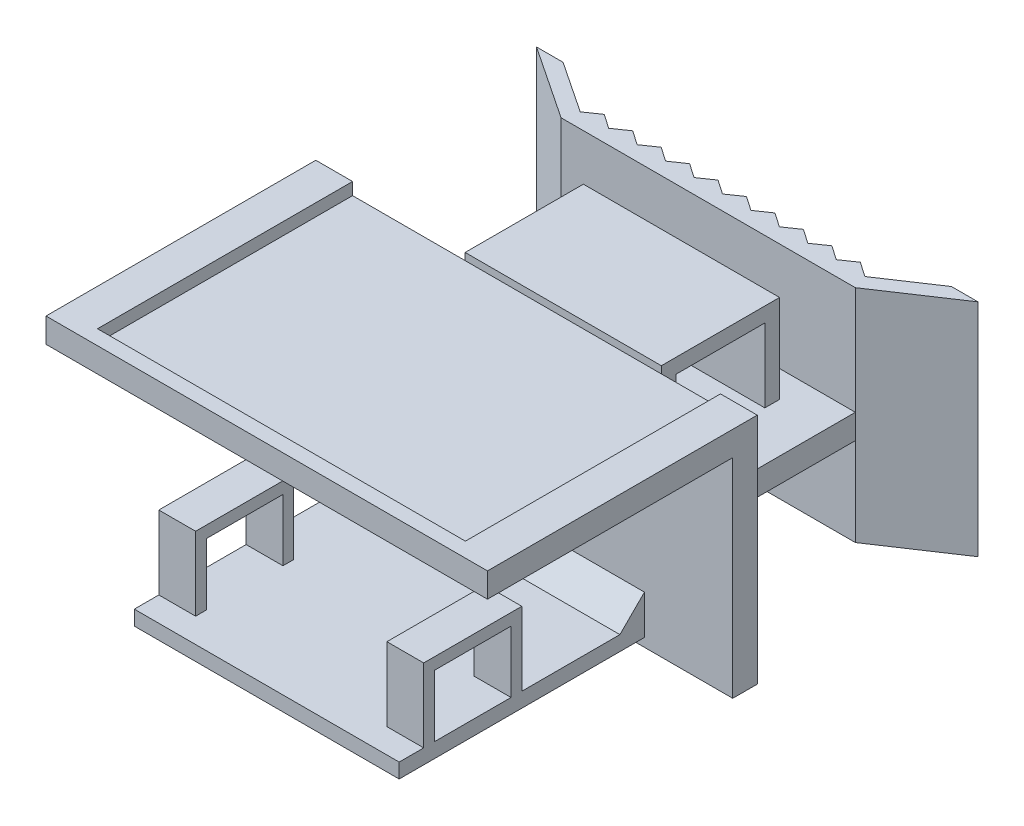
SolidWorks part; units mm, degrees
ref_plane "Alzado" through (0, 0, 0) normal (0, 0, 1) x (1, 0, 0)
ref_plane "Planta" through (0, 0, 0) normal (0, 1, 0) x (1, 0, 0)
ref_plane "Vista lateral" through (0, 0, 0) normal (1, 0, 0) x (0, 0, -1)
sketch "Croquis1" plane through (0, 0, 0) normal (0, 1, 0) x (1, 0, 0)
  line L1 (-45, 25) -> (45, 25)
  line L2 (-45, 25) -> (-45, -25)
  line L3 (-45, -25) -> (45, -25)
  line L4 (45, 25) -> (45, -25)
  line L5 (-45, 25) -> (45, -25) construction
  line L6 (-45, -25) -> (45, 25) construction
  point P0 (0, 0)
  dimension "D1" = 50
  dimension "D2" = 90
extrude "Saliente-Extruir1" add sketch "Croquis1" along normal blind 5
sketch "Croquis4" plane through (0, 5, 0) normal (0, 1, 0) x (1, 0, 0)
  line L0 (45, -25) -> (45, 25) construction
  line L1 (-45, 25) -> (45, 25)
  line L2 (-45, 25) -> (-45, 30)
  line L3 (-45, 30) -> (45, 30)
  line L4 (45, 25) -> (45, 30)
  dimension "D1" = 5
extrude "Saliente-Extruir2" add sketch "Croquis4" against normal blind 49.5
sketch "Croquis5" plane through (0, 0, -30) normal (0, 0, -1) x (-1, 0, 0)
  line L0 (-45, -44.5) -> (45, -44.5) construction
  line L1 (-30, -19.5) -> (30, -19.5)
  line L2 (-30, -19.5) -> (-30, -24.5)
  line L3 (-30, -24.5) -> (30, -24.5)
  line L4 (30, -19.5) -> (30, -24.5)
  line L5 (-30, -19.5) -> (30, -24.5) construction
  line L6 (-30, -24.5) -> (30, -19.5) construction
  point P0 (0, -22)
  dimension "D1" = 60
  dimension "D2" = 5
  dimension "D3" = 20
extrude "Saliente-Extruir3" add sketch "Croquis5" along normal blind 35
sketch "Croquis7" plane through (0, -19.5, 0) normal (0, 1, 0) x (1, 0, 0)
  line L4 (-30, 30) -> (30, 30)
  line L5 (30, 30) -> (30, 65)
  line L6 (30, 65) -> (-30, 65)
  line L7 (-30, 65) -> (-30, 30)
  line L8 (-30, 30) -> (30, 30)
  line L9 (30, 30) -> (30, 65)
  line L10 (30, 65) -> (-30, 65)
  line L11 (-30, 65) -> (-30, 30)
  dimension "D1" = 0
sketch "Croquis11" plane through (0, 5, 0) normal (0, 1, 0) x (1, 0, 0)
  line L1 (-37.5, 58) -> (37.5, 58)
  line L2 (-37.5, 58) -> (-37.5, -22)
  line L3 (-37.5, -22) -> (37.5, -22)
  line L4 (37.5, 58) -> (37.5, -22)
  line L6 (-45, -25) -> (45, -25) construction
  point P4 (0, -22)
  dimension "D1" = 75
  dimension "D2" = 80
  dimension "D3" = 3
extrude "Cortar-Extruir3" cut sketch "Croquis11" against normal blind 2.5
sketch "Croquis12" plane through (0, -19.5, 0) normal (0, 1, 0) x (1, 0, 0)
  line L0 (-45, 30) -> (-45, -25) construction
  line L1 (-45, 65) -> (45, 65) construction
  line L2 (-45, 65) -> (-45, 75) construction
  line L3 (-45, 75) -> (-39.5917, 75) construction
  line L4 (45, 65) -> (45, 75) construction
  line L5 (45, -25) -> (45, 30) construction
  line L6 (30, 65) -> (-30, 65) construction
  line L7 (-45, 75) -> (-30, 65)
  line L8 (30, 65) -> (45, 75)
  line L9 (-30, 65) -> (30, 65)
  line L10 (-39.5917, 75) -> (-29.0917, 68)
  line L11 (-29.0917, 68) -> (29.0917, 68)
  line L12 (29.0917, 68) -> (39.5917, 75)
  line L13 (-45, 75) -> (-39.5917, 75)
  line L14 (-43.3359, 77.4962) -> (-29.0917, 68) construction
  line L15 (39.5917, 75) -> (45, 75) construction
  line L16 (39.5917, 75) -> (45, 75)
  line L17 (29.0917, 68) -> (43.3359, 77.4962) construction
  line L18 (-29.0917, 68) -> (-26.1917, 70)
  line L19 (-26.1917, 70) -> (-23.2917, 68)
  line L20 (0, 68) -> (0, 75) construction
  line L21 (-20.3917, 70) -> (-17.4917, 68)
  line L22 (-23.2917, 68) -> (-20.3917, 70)
  line L23 (-14.5917, 70) -> (-11.6917, 68)
  line L24 (-17.4917, 68) -> (-14.5917, 70)
  line L25 (-8.7917, 70) -> (-5.8917, 68)
  line L26 (-11.6917, 68) -> (-8.7917, 70)
  line L27 (-2.9917, 70) -> (-0.0917, 68)
  line L28 (-5.8917, 68) -> (-2.9917, 70)
  line L29 (2.8083, 70) -> (5.7083, 68)
  line L30 (-0.0917, 68) -> (2.8083, 70)
  line L31 (8.6083, 70) -> (11.5083, 68)
  line L32 (5.7083, 68) -> (8.6083, 70)
  line L33 (14.4083, 70) -> (17.3083, 68)
  line L34 (11.5083, 68) -> (14.4083, 70)
  line L35 (20.2083, 70) -> (23.1083, 68)
  line L36 (17.3083, 68) -> (20.2083, 70)
  line L37 (26.0083, 70) -> (28.9083, 68)
  line L38 (23.1083, 68) -> (26.0083, 70)
  line M15 (30, 65) -> (-30, 65)
  dimension "D1" = 10
  dimension "D2" = 3
  dimension "D3" = 2
  dimension "D4" = 2.9
  dimension "D5" = 2.9
  dimension "D6" = 10
extrude "Saliente-Extruir4" add sketch "Croquis12" against normal up to surface and the other way up to surface contours L16 L12 L11 L10 L13 L7 L8 M15 | L19 L18 L11 | L22 L11 L21 | L24 L11 L23 | L28 L11 L27 | L30 L11 L29 | L26 L11 L25 | L32 L11 L31 | L34 L11 L33 | L36 L11 L35 | L38 L11 L37
sketch "Croquis13" plane through (0, -44.5, 0) normal (0, -1, 0) x (1, 0, 0)
  line L4 (-45, -25) -> (-45, -30)
  line L5 (-45, -30) -> (45, -30)
  line L6 (45, -30) -> (45, -25)
  line L7 (45, -25) -> (-45, -25)
  line L8 (-45, -25) -> (-45, -30)
  line L9 (-45, -30) -> (45, -30)
  line L10 (45, -30) -> (45, -25)
  line L11 (45, -25) -> (-45, -25)
  line L36 (-39.5917, -75) -> (-29.0917, -68)
  line L37 (-29.0917, -68) -> (-26.1917, -70)
  line L38 (-26.1917, -70) -> (-23.2917, -68)
  line L39 (-23.2917, -68) -> (-20.3917, -70)
  line L40 (-20.3917, -70) -> (-17.4917, -68)
  line L41 (-17.4917, -68) -> (-14.5917, -70)
  line L42 (-14.5917, -70) -> (-11.6917, -68)
  line L43 (-11.6917, -68) -> (-8.7917, -70)
  line L44 (-8.7917, -70) -> (-5.8917, -68)
  line L45 (-5.8917, -68) -> (-2.9917, -70)
  line L46 (-2.9917, -70) -> (-0.0917, -68)
  line L47 (-0.0917, -68) -> (2.8083, -70)
  line L48 (2.8083, -70) -> (5.7083, -68)
  line L49 (5.7083, -68) -> (8.6083, -70)
  line L50 (8.6083, -70) -> (11.5083, -68)
  line L51 (11.5083, -68) -> (14.4083, -70)
  line L52 (14.4083, -70) -> (17.3083, -68)
  line L53 (17.3083, -68) -> (20.2083, -70)
  line L54 (20.2083, -70) -> (23.1083, -68)
  line L55 (23.1083, -68) -> (26.0083, -70)
  line L56 (26.0083, -70) -> (28.9083, -68)
  line L57 (28.9083, -68) -> (29.0917, -68)
  line L58 (29.0917, -68) -> (39.5917, -75)
  line L59 (39.5917, -75) -> (45, -75)
  line L60 (45, -75) -> (30, -65)
  line L61 (30, -65) -> (-30, -65)
  line L62 (-30, -65) -> (-45, -75)
  line L63 (-45, -75) -> (-39.5917, -75)
  line L64 (-39.5917, -75) -> (-29.0917, -68)
  line L65 (-29.0917, -68) -> (-26.1917, -70)
  line L66 (-26.1917, -70) -> (-23.2917, -68)
  line L67 (-23.2917, -68) -> (-20.3917, -70)
  line L68 (-20.3917, -70) -> (-17.4917, -68)
  line L69 (-17.4917, -68) -> (-14.5917, -70)
  line L70 (-14.5917, -70) -> (-11.6917, -68)
  line L71 (-11.6917, -68) -> (-8.7917, -70)
  line L72 (-8.7917, -70) -> (-5.8917, -68)
  line L73 (-5.8917, -68) -> (-2.9917, -70)
  line L74 (-2.9917, -70) -> (-0.0917, -68)
  line L75 (-0.0917, -68) -> (2.8083, -70)
  line L76 (2.8083, -70) -> (5.7083, -68)
  line L77 (5.7083, -68) -> (8.6083, -70)
  line L78 (8.6083, -70) -> (11.5083, -68)
  line L79 (11.5083, -68) -> (14.4083, -70)
  line L80 (14.4083, -70) -> (17.3083, -68)
  line L81 (17.3083, -68) -> (20.2083, -70)
  line L82 (20.2083, -70) -> (23.1083, -68)
  line L83 (23.1083, -68) -> (26.0083, -70)
  line L84 (26.0083, -70) -> (28.9083, -68)
  line L85 (28.9083, -68) -> (29.0917, -68)
  line L86 (29.0917, -68) -> (39.5917, -75)
  line L87 (39.5917, -75) -> (45, -75)
  line L88 (45, -75) -> (30, -65)
  line L89 (30, -65) -> (-30, -65)
  line L90 (-30, -65) -> (-45, -75)
  line L91 (-45, -75) -> (-39.5917, -75)
  dimension "D1" = 0
  dimension "D2" = 0
extrude "Cortar-Extruir4" cut sketch "Croquis13" against normal blind 1
sketch "Croquis15" plane through (0, 0, -25) normal (0, 0, 1) x (1, 0, 0)
  line L0 (-45, -43.5) -> (-45, 0) construction
  line L1 (-27, -37.75) -> (27, -37.75)
  line L2 (-27, -37.75) -> (-27, -40.75)
  line L3 (-27, -40.75) -> (27, -40.75)
  line L4 (27, -37.75) -> (27, -40.75)
  line L5 (45, -43.5) -> (45, 0) construction
  line L6 (45, 0) -> (45, -43.5) construction
  line L7 (45, -21.75) -> (-45, -21.75) construction
  dimension "D1" = 3
  dimension "D2" = 18
  dimension "D3" = 18
  dimension "D4" = 16
extrude "Saliente-Extruir5" add sketch "Croquis15" along normal up to surface (50 mm away) up to face at (0, 2.5, 25)
sketch "Croquis18" plane through (0, -43.5, 0) normal (0, -1, 0) x (1, 0, 0)
  line L8 (45, -25) -> (-45, -25)
  line L9 (-45, -25) -> (-45, -30)
  line L10 (-45, -30) -> (45, -30)
  line L11 (45, -30) -> (45, -25)
  line L12 (45, -25) -> (-45, -25)
  line L13 (-45, -25) -> (-45, -30)
  line L14 (-45, -30) -> (45, -30)
  line L15 (45, -30) -> (45, -25)
  line L40 (-45, -75) -> (-39.5917, -75)
  line L41 (-39.5917, -75) -> (-29.0917, -68)
  line L42 (-29.0917, -68) -> (-26.1917, -70)
  line L43 (-26.1917, -70) -> (-23.2917, -68)
  line L44 (-23.2917, -68) -> (-20.3917, -70)
  line L45 (-20.3917, -70) -> (-17.4917, -68)
  line L46 (-17.4917, -68) -> (-14.5917, -70)
  line L47 (-14.5917, -70) -> (-11.6917, -68)
  line L48 (-11.6917, -68) -> (-8.7917, -70)
  line L49 (-8.7917, -70) -> (-5.8917, -68)
  line L50 (-5.8917, -68) -> (-2.9917, -70)
  line L51 (-2.9917, -70) -> (-0.0917, -68)
  line L52 (-0.0917, -68) -> (2.8083, -70)
  line L53 (2.8083, -70) -> (5.7083, -68)
  line L54 (5.7083, -68) -> (8.6083, -70)
  line L55 (8.6083, -70) -> (11.5083, -68)
  line L56 (11.5083, -68) -> (14.4083, -70)
  line L57 (14.4083, -70) -> (17.3083, -68)
  line L58 (17.3083, -68) -> (20.2083, -70)
  line L59 (20.2083, -70) -> (23.1083, -68)
  line L60 (23.1083, -68) -> (26.0083, -70)
  line L61 (26.0083, -70) -> (28.9083, -68)
  line L62 (28.9083, -68) -> (29.0917, -68)
  line L63 (29.0917, -68) -> (39.5917, -75)
  line L64 (39.5917, -75) -> (45, -75)
  line L65 (45, -75) -> (30, -65)
  line L66 (30, -65) -> (-30, -65)
  line L67 (-30, -65) -> (-45, -75)
  line L68 (-45, -75) -> (-39.5917, -75)
  line L69 (-39.5917, -75) -> (-29.0917, -68)
  line L70 (-29.0917, -68) -> (-26.1917, -70)
  line L71 (-26.1917, -70) -> (-23.2917, -68)
  line L72 (-23.2917, -68) -> (-20.3917, -70)
  line L73 (-20.3917, -70) -> (-17.4917, -68)
  line L74 (-17.4917, -68) -> (-14.5917, -70)
  line L75 (-14.5917, -70) -> (-11.6917, -68)
  line L76 (-11.6917, -68) -> (-8.7917, -70)
  line L77 (-8.7917, -70) -> (-5.8917, -68)
  line L78 (-5.8917, -68) -> (-2.9917, -70)
  line L79 (-2.9917, -70) -> (-0.0917, -68)
  line L80 (-0.0917, -68) -> (2.8083, -70)
  line L81 (2.8083, -70) -> (5.7083, -68)
  line L82 (5.7083, -68) -> (8.6083, -70)
  line L83 (8.6083, -70) -> (11.5083, -68)
  line L84 (11.5083, -68) -> (14.4083, -70)
  line L85 (14.4083, -70) -> (17.3083, -68)
  line L86 (17.3083, -68) -> (20.2083, -70)
  line L87 (20.2083, -70) -> (23.1083, -68)
  line L88 (23.1083, -68) -> (26.0083, -70)
  line L89 (26.0083, -70) -> (28.9083, -68)
  line L90 (28.9083, -68) -> (29.0917, -68)
  line L91 (29.0917, -68) -> (39.5917, -75)
  line L92 (39.5917, -75) -> (45, -75)
  line L93 (45, -75) -> (30, -65)
  line L94 (30, -65) -> (-30, -65)
  line L95 (-30, -65) -> (-45, -75)
  dimension "D1" = 0
  dimension "D2" = 0
extrude "Cortar-Extruir5" cut sketch "Croquis18" against normal blind 1
sketch "Croquis22" plane through (0, 0, 0) normal (1, 0, 0) x (0, 0, -1)
  line L0 (25, -37.75) -> (25, -32.75)
  line L1 (25, -42.5) -> (25, 0) construction
  line L2 (25, -32.75) -> (20, -37.75)
  line L3 (-25, -37.75) -> (25, -37.75) construction
  line L4 (20, -37.75) -> (25, -37.75)
  dimension "D1" = 5
  dimension "D2" = 5
extrude "Saliente-Extruir6" add sketch "Croquis22" against normal up to surface and the other way up to surface up to face at (-27, -39.25, 0) other way up to face at (27, -39.25, 0)
sketch "Croquis23" plane through (0, 0, 0) normal (1, 0, 0) x (0, 0, -1)
  line L0 (65, -19.5) -> (30, -19.5) construction
  line L1 (38.45, -4.5) -> (56.55, -4.5)
  line L2 (38.45, -4.5) -> (38.45, -19.5)
  line L4 (56.55, -4.5) -> (56.55, -19.5)
  line L5 (38.45, -4.5) -> (56.55, -19.5) construction
  line L6 (38.45, -19.5) -> (56.55, -4.5) construction
  line L7 (35.45, -1.5) -> (35.45, -19.5)
  line L9 (59.55, -1.5) -> (59.55, -19.5)
  line L10 (35.45, -1.5) -> (59.55, -1.5)
  line L11 (38.45, -19.5) -> (35.45, -19.5)
  line L12 (56.55, -19.5) -> (59.55, -19.5)
  line L13 (35.45, -1.5) -> (35.45, -22.5) construction
  line L14 (35.45, -22.5) -> (59.55, -22.5) construction
  line L15 (59.55, -1.5) -> (59.55, -22.5) construction
  line L16 (38.45, -19.5) -> (56.55, -19.5) construction
  point P0 (47.5, -12)
  point P7 (47.5, -19.5)
  point P12 (47.5, -1.5)
  dimension "D1" = 15
  dimension "D2" = 18.1
  dimension "D3" = 3
extrude "Saliente-Extruir7" add sketch "Croquis23" along normal mid plane 40
sketch "Croquis24" plane through (-27, 0, 0) normal (-1, 0, 0) x (0, 0, 1)
  line L0 (25, -37.75) -> (-20, -37.75) construction
  line L1 (20, -37.75) -> (0, -37.75)
  line L2 (20, -37.75) -> (20, -22.75)
  line L3 (20, -22.75) -> (0, -22.75)
  line L4 (0, -37.75) -> (0, -22.75)
  line L5 (25, -40.75) -> (25, -37.75) construction
  dimension "D1" = 15
  dimension "D2" = 20
  dimension "D3" = 5
extrude "Saliente-Extruir8" add sketch "Croquis24" against normal blind 54 contours L2 L3 L4 L1
sketch "Croquis25" plane through (-27, 0, 0) normal (-1, 0, 0) x (0, 0, 1)
  line L0 (0, -37.75) -> (-20, -37.75) construction
  line L1 (2.2, -37.75) -> (17.8, -37.75)
  line L2 (2.2, -37.75) -> (2.2, -25.15)
  line L3 (2.2, -25.15) -> (17.8, -25.15)
  line L4 (17.8, -37.75) -> (17.8, -25.15)
  line L5 (20, -37.75) -> (20, -22.75) construction
  dimension "D1" = 15.6
  dimension "D2" = 12.6
  dimension "D3" = 2.2
extrude "Cortar-Extruir6" cut sketch "Croquis25" against normal blind 54
sketch "Croquis26" plane through (0, 0, 20) normal (0, 0, 1) x (1, 0, 0)
  line L0 (27, -22.75) -> (-27, -22.75) construction
  line L1 (-19.5, -22.75) -> (19.5, -22.75)
  line L2 (-19.5, -22.75) -> (-19.5, -37.75)
  line L3 (-19.5, -37.75) -> (19.5, -37.75)
  line L4 (19.5, -22.75) -> (19.5, -37.75)
  line L5 (27, -37.75) -> (-27, -37.75) construction
  line L6 (-27, -37.75) -> (-27, -22.75) construction
  line L7 (27, -37.75) -> (27, -22.75) construction
  point P12 (27, -30.25)
  dimension "D1" = 7.5
  dimension "D2" = 7.5
extrude "Cortar-Extruir7" cut sketch "Croquis26" against normal blind 20
